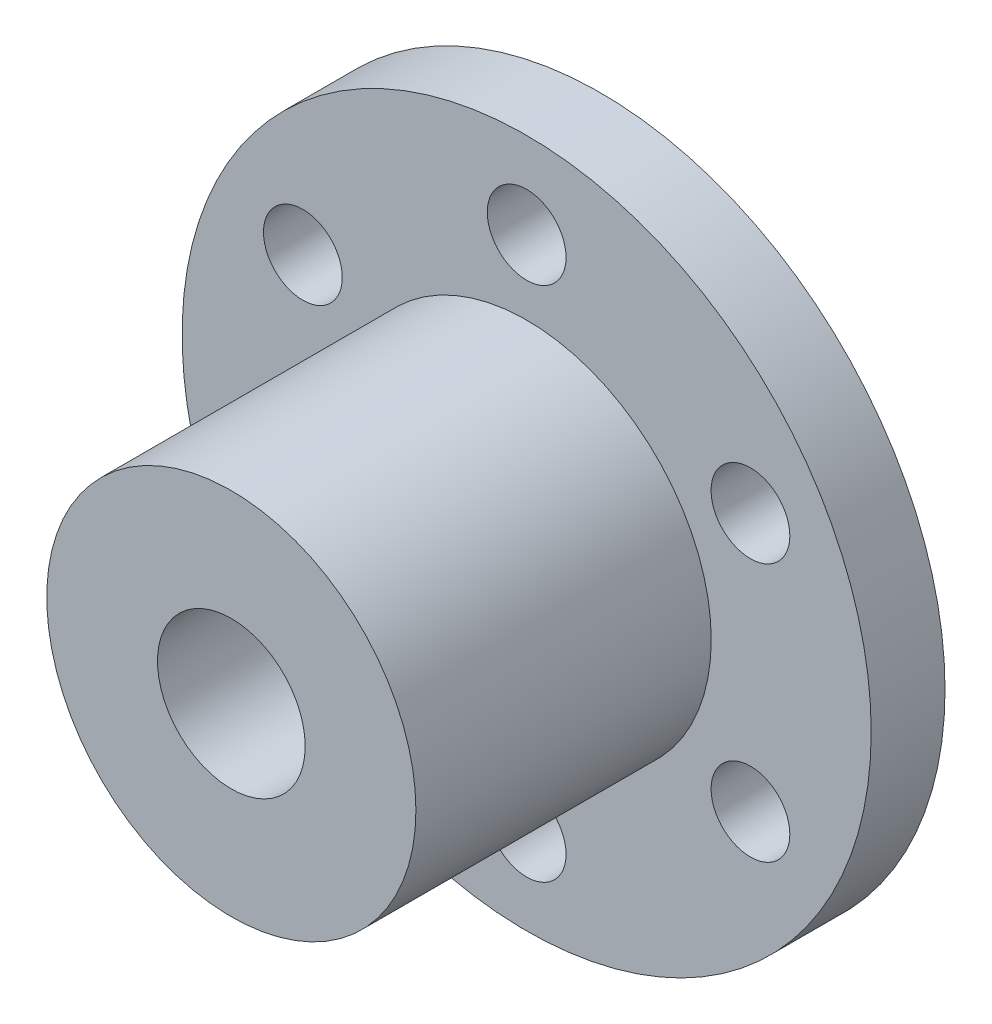
SolidWorks part; units mm, degrees
ref_plane "前视基准面" through (0, 0, 0) normal (0, 0, 1) x (1, 0, 0)
ref_plane "上视基准面" through (0, 0, 0) normal (0, 1, 0) x (1, 0, 0)
ref_plane "右视基准面" through (0, 0, 0) normal (1, 0, 0) x (0, 0, -1)
sketch "草图1" plane through (0, 0, 0) normal (0, 0, 1) x (1, 0, 0)
  circle A0 centre (0, 0) radius 14
  dimension "D1" = 28
extrude "凸台-拉伸1" add sketch "草图1" along normal blind 3
sketch "草图2" plane through (0, 0, 3) normal (0, 0, 1) x (1, 0, 0)
  circle A0 centre (0, 0) radius 7.5
  circle A1 centre (0, 0) radius 3
  dimension "D1" = 15
  dimension "D2" = 6
extrude "凸台-拉伸2" add sketch "草图2" along normal blind 12
sketch "草图3" plane through (0, 0, 3) normal (0, 0, 1) x (1, 0, 0)
  circle A0 centre (0, 0) radius 3
extrude "切除-拉伸1" cut sketch "草图3" against normal through all
sketch "草图4" plane through (0, 0, 0) normal (0, 0, -1) x (-1, 0, 0)
  circle A0 centre (-9.0933, -5.25) radius 1.6
  circle A1 centre (9.0933, 5.25) radius 1.6
  circle A2 centre (0, -10.5) radius 1.6
  circle A3 centre (9.0933, -5.25) radius 1.6
  circle A4 centre (0, 10.5) radius 1.6
  circle A5 centre (-9.0933, 5.25) radius 1.6
extrude "切除-拉伸2" cut sketch "草图4" against normal through all
